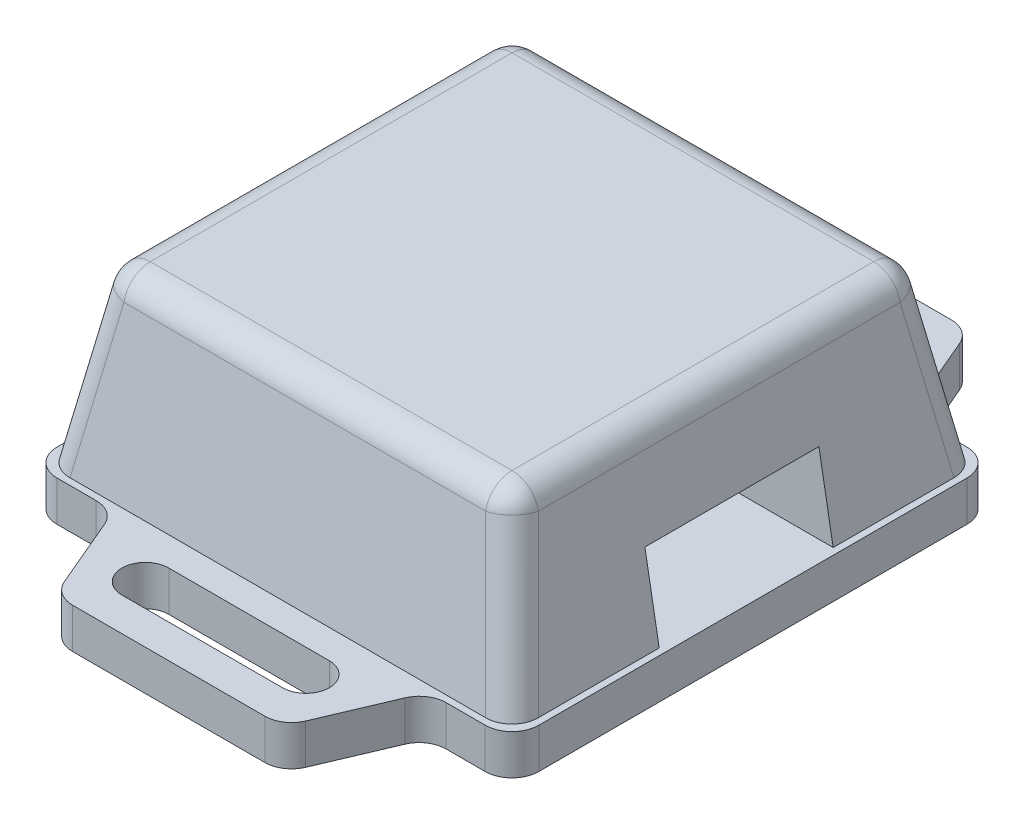
SolidWorks part; units mm, degrees
ref_plane "Front" through (0, 0, 0) normal (0, 0, 1) x (1, 0, 0)
ref_plane "Top" through (0, 0, 0) normal (0, 1, 0) x (1, 0, 0)
ref_plane "Right" through (0, 0, 0) normal (1, 0, 0) x (0, 0, -1)
sketch "草图1" plane through (0, 0, 0) normal (0, 1, 0) x (1, 0, 0)
  line L0 (0, 36.1132) -> (0, -38.6038) construction
  line L1 (-66, 0) -> (60.9057, 0) construction
  line L3 (-18, -25.65) -> (18, -25.65)
  line L4 (-18, -25.65) -> (-18, 25.65)
  line L5 (-18, 25.65) -> (18, 25.65)
  line L6 (18, -25.65) -> (18, 25.65)
  line L7 (-18, -25.65) -> (18, 25.65) construction
  line L8 (-18, 25.65) -> (18, -25.65) construction
  point P5 (0, 0)
  dimension "D1" = 36
  dimension "D2" = 51.3
extrude "凸台-拉伸1" add sketch "草图1" along normal blind 3
sketch "草图2" plane through (0, 3, 0) normal (0, 1, 0) x (1, 0, 0)
  line L0 (0, 36.3674) -> (0, -34.1593) construction
  line L1 (-30.133, 0) -> (32.9904, 0) construction
  line L2 (-6, 21.4) -> (6, 21.4) construction
  line L3 (-6, 23.15) -> (6, 23.15)
  line L4 (-6, 19.65) -> (6, 19.65)
  line L5 (-6, -21.4) -> (6, -21.4) construction
  line L6 (-6, -23.15) -> (6, -23.15)
  line L7 (-6, -19.65) -> (6, -19.65)
  arc A0 (-6, 23.15) -> (-6, 19.65) centre (-6, 21.4) ccw
  arc A1 (6, 19.65) -> (6, 23.15) centre (6, 21.4) ccw
  arc A2 (-6, -23.15) -> (-6, -19.65) centre (-6, -21.4) cw
  arc A3 (6, -19.65) -> (6, -23.15) centre (6, -21.4) cw
  point P7 (0, 21.4)
  point P14 (0, -21.4)
  dimension "D1" = 12
  dimension "D2" = 3.5
  dimension "D3" = 42.8
extrude "切除-拉伸1" cut sketch "草图2" against normal blind 3
sketch "草图4" plane through (0, 3, 0) normal (0, 1, 0) x (1, 0, 0)
  line L0 (0, 31.0983) -> (0, -33.1571) construction
  line L1 (-26.2223, 0) -> (22.3214, 0) construction
  line L3 (-17.5, -17.5) -> (17.5, -17.5)
  line L4 (-17.5, -17.5) -> (-17.5, 17.5)
  line L5 (-17.5, 17.5) -> (17.5, 17.5)
  line L6 (17.5, -17.5) -> (17.5, 17.5)
  line L7 (-17.5, -17.5) -> (17.5, 17.5) construction
  line L8 (-17.5, 17.5) -> (17.5, -17.5) construction
  point P5 (0, 0)
  dimension "D1" = 35
  dimension "D2" = 35
ref_plane "基准面1" through (0, 16, 0) normal (0, 1, 0) x (1, 0, 0)
sketch "草图5" plane through (0, 16, 0) normal (0, 1, 0) x (1, 0, 0)
  line L0 (0, 47.0158) -> (0, -46.143) construction
  line L1 (-37.6179, 0) -> (33.2284, 0) construction
  line L3 (-15.19, -15.19) -> (15.19, -15.19)
  line L4 (-15.19, -15.19) -> (-15.19, 15.19)
  line L5 (-15.19, 15.19) -> (15.19, 15.19)
  line L6 (15.19, -15.19) -> (15.19, 15.19)
  line L7 (-15.19, -15.19) -> (15.19, 15.19) construction
  line L8 (-15.19, 15.19) -> (15.19, -15.19) construction
  point P5 (0, 0)
  dimension "D1" = 30.38
  dimension "D2" = 30.38
loft "放样1" add profiles "草图5", "草图4"
fillet "圆角1" radius 2 8 edges
sketch "草图6" plane through (0, 3, 0) normal (0, 1, 0) x (1, 0, 0)
  line L0 (0, 33.2546) -> (0, -31.4667) construction
  line L1 (-33.3738, 0) -> (26.3414, 0) construction
  line L2 (-8.5, 25.65) -> (-11.75, 18)
  line L3 (18, 25.65) -> (-18, 25.65) construction
  line L4 (-11.75, 18) -> (-18, 18)
  line L5 (-18, 25.65) -> (-18, -25.65) construction
  line L6 (-18, 18) -> (-18, 25.65)
  line L7 (-18, 25.65) -> (-8.5, 25.65)
  line L8 (18, 25.65) -> (8.5, 25.65)
  line L9 (18, 18) -> (18, 25.65)
  line L10 (11.75, 18) -> (18, 18)
  line L11 (8.5, 25.65) -> (11.75, 18)
  line L12 (8.5, -25.65) -> (11.75, -18)
  line L13 (11.75, -18) -> (18, -18)
  line L14 (18, -18) -> (18, -25.65)
  line L15 (18, -25.65) -> (8.5, -25.65)
  line L16 (-18, -25.65) -> (-8.5, -25.65)
  line L17 (-18, -18) -> (-18, -25.65)
  line L18 (-11.75, -18) -> (-18, -18)
  line L19 (-8.5, -25.65) -> (-11.75, -18)
  dimension "D1" = 23.5
  dimension "D2" = 36
  dimension "D3" = 17
extrude "切除-拉伸3" cut sketch "草图6" against normal blind 13
fillet "圆角2" radius 2 12 edges at (8.5, 1.5, -25.65) (11.75, 1.5, -18) (18, 1.5, -18) (18, 1.5, 18) (11.75, 1.5, 18) (8.5, 1.5, 25.65) (-8.5, 1.5, 25.65) (-11.75, 1.5, 18) (-18, 1.5, 18) (-18, 1.5, -18) (-11.75, 1.5, -18) (-8.5, 1.5, -25.65)
sketch "草图8" plane through (0, 0, 0) normal (0, -1, 0) x (1, 0, 0)
  line L0 (0, 33.9697) -> (0, -33.9697) construction
  line L1 (-26.2223, 0) -> (26.1031, 0) construction
  line L3 (-11.75, -11.75) -> (11.75, -11.75) construction
  line L4 (-11.75, -11.75) -> (-11.75, 11.75) construction
  line L5 (-11.75, 11.75) -> (11.75, 11.75) construction
  line L6 (11.75, -11.75) -> (11.75, 11.75) construction
  line L7 (-11.75, -11.75) -> (11.75, 11.75) construction
  line L8 (-11.75, 11.75) -> (11.75, -11.75) construction
  circle A0 centre (-11.75, 11.75) radius 2.75
  circle A1 centre (11.75, -11.75) radius 2.75
  point P5 (0, 0)
  dimension "D3" = 5.5
  dimension "D4" = 5.5
  dimension "D1" = 23.5
  dimension "D2" = 23.5
extrude "切除-拉伸4" cut sketch "草图8" against normal blind 0.5
hole_wizard "大小mm 暗销孔2" positions "草图14" profile "草图15" hole size "Ø2.0" standard "GB"
sketch "草图14" plane through (0, 0, 0) normal (0, -1, 0) x (-1, 0, 0)
  point P0 (11.75, -11.75)
  point P3 (-11.75, 11.75)
sketch "草图15" plane through (-11.75, 0, 11.75) normal (1, 0, 0) x (0, 0, -1)
  line L0 (0, 0) -> (0, 5.6009)
  line L1 (0, 5.6009) -> (1, 5)
  line L2 (1, 5) -> (1, 0)
  line L5 (1, 0) -> (0, 0)
  line L10 (0, 5.6009) -> (-1, 5) construction
  line L11 (0, -6.35) -> (0, 107.95) construction
  dimension "孔直径" = 2
  dimension "孔深度" = 5
  dimension "导头角度" = 118
sketch "草图16" plane through (0, 0, 0) normal (1, 0, 0) x (0, 0, -1)
  line L0 (0, 23.4784) -> (0, -5.8154) construction
  line L1 (-32.9396, 0) -> (32.8756, 0) construction
  line L2 (-38.1204, 3) -> (37.6087, 3) construction
  line L4 (-6.5, 3) -> (6.5, 3)
  line L5 (-6.5, 3) -> (-6.5, 9)
  line L6 (-6.5, 9) -> (6.5, 9)
  line L7 (6.5, 3) -> (6.5, 9)
  dimension "D1" = 3
  dimension "D2" = 13
  dimension "D3" = 6
extrude "切除-拉伸5" cut sketch "草图16" along normal through all from offset 10
